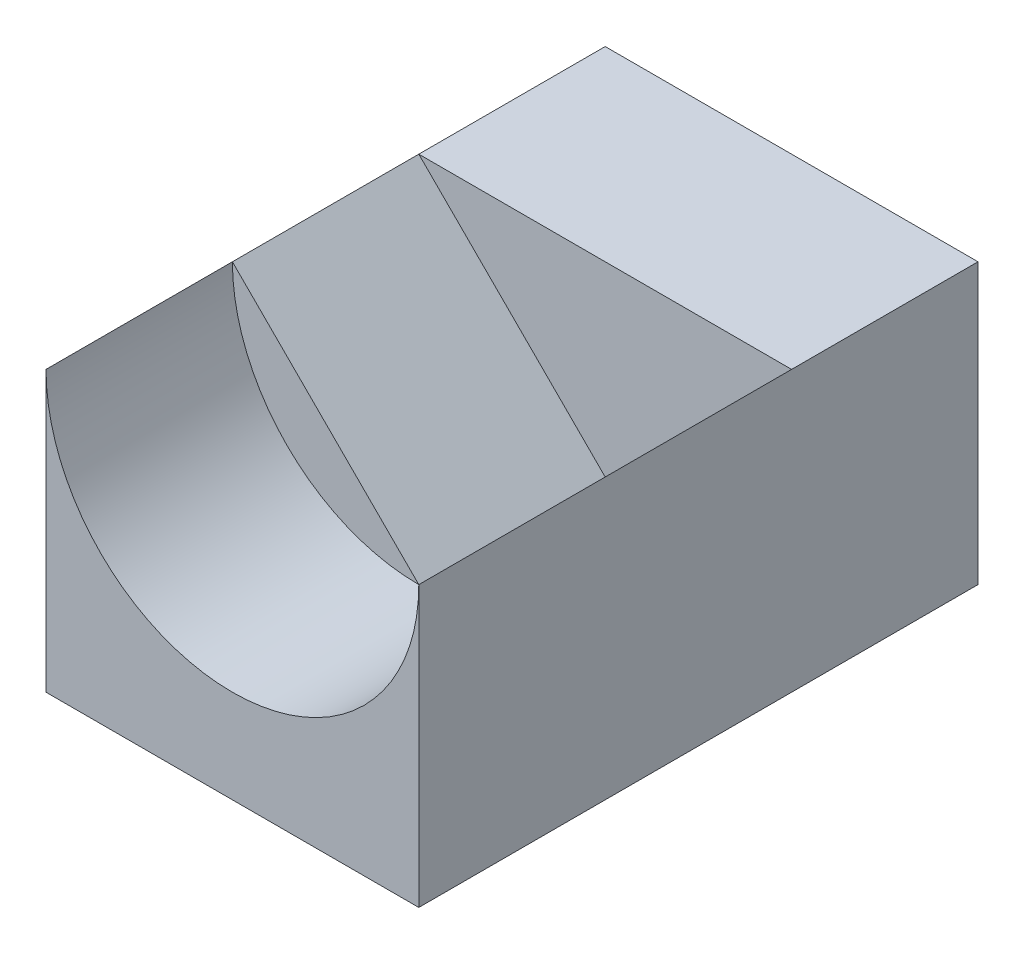
SolidWorks part; units mm, degrees
ref_plane "前基準面" through (0, 0, 0) normal (0, 0, 1) x (1, 0, 0)
ref_plane "上基準面" through (0, 0, 0) normal (0, 1, 0) x (1, 0, 0)
ref_plane "右基準面" through (0, 0, 0) normal (1, 0, 0) x (0, 0, -1)
sketch "草圖1" plane through (0, 0, 0) normal (0, 1, 0) x (1, 0, 0)
  line L1 (10, 15) -> (-10, 15)
  line L2 (10, 15) -> (10, -15)
  line L3 (10, -15) -> (-10, -15)
  line L4 (-10, 15) -> (-10, -15)
  line L5 (10, 15) -> (-10, -15) construction
  line L6 (10, -15) -> (-10, 15) construction
  point P0 (0, 0)
  dimension "D1" = 30
  dimension "D2" = 20
extrude "填料-伸長1" add sketch "草圖1" along normal blind 15
sketch "草圖2" plane through (0, 0, 15) normal (0, 0, 1) x (1, 0, 0)
  line L0 (-10, 15) -> (10, 15) construction
  line L1 (10, 15) -> (-10, 15)
  arc A0 (-10, 15) -> (10, 15) centre (0, 15) ccw
extrude "除料-伸長1" cut sketch "草圖2" against normal blind 10 contours A0 L1
sketch "草圖3" plane through (0, 0, 5) normal (0, 0, 1) x (1, 0, 0)
  line L0 (-10, 15) -> (0, 5)
  line L1 (0, 5) -> (10, 15)
  line L2 (10, 15) -> (-10, 15)
  arc A0 (-10, 15) -> (10, 15) centre (0, 15) ccw construction
extrude "除料-伸長2" cut sketch "草圖3" against normal blind 10
scale "縮放比例1" scale about centroid uniform scaling yes scale factor 0.2
